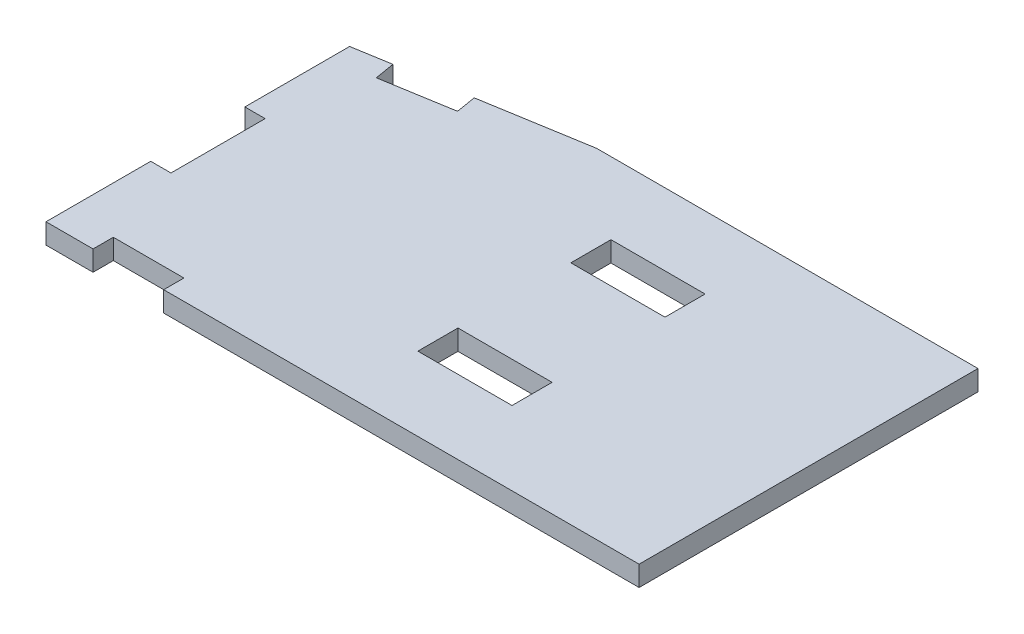
SolidWorks part; units mm, degrees
ref_plane "Front Plane" through (0, 0, 0) normal (0, 0, 1) x (1, 0, 0)
ref_plane "Top Plane" through (0, 0, 0) normal (0, 1, 0) x (1, 0, 0)
ref_plane "Right Plane" through (0, 0, 0) normal (1, 0, 0) x (0, 0, -1)
sketch "Sketch1" plane through (0, 0, 0) normal (0, 1, 0) x (1, 0, 0)
  line L0 (-99.45, 35.936) -> (-42.3, 45.461)
  line L1 (-47.5, 40) -> (47.5, 40)
  line L2 (-55, 32.5) -> (-55, -32.5)
  line L3 (-47.5, -40) -> (47.5, -40)
  line L4 (55, 32.5) -> (55, -32.5)
  line L5 (-55, 40) -> (55, -40) construction
  line L6 (-55, -40) -> (55, 40) construction
  line L7 (-99.45, 45.461) -> (60.57, 45.461)
  line L8 (-99.45, 45.461) -> (-99.45, -45.979)
  line L9 (-99.45, -45.979) -> (60.57, -45.979)
  line L10 (60.57, 45.461) -> (60.57, -45.979)
  line L11 (-99.45, 45.461) -> (60.57, -45.979) construction
  line L12 (-99.45, -45.979) -> (60.57, 45.461) construction
  arc A0 (47.5, -40) -> (55, -32.5) centre (47.5, -32.5) ccw
  arc A1 (55, 32.5) -> (47.5, 40) centre (47.5, 32.5) ccw
  arc A2 (-47.5, 40) -> (-55, 32.5) centre (-47.5, 32.5) ccw
  arc A3 (-47.5, -40) -> (-55, -32.5) centre (-47.5, -32.5) cw
  point P0 (0, 0)
  point P18 (0, 0)
  dimension "D3" = 7.5
  dimension "D1" = 80
  dimension "D2" = 110
  dimension "D4" = 5.461
  dimension "D5" = 44.45
  dimension "D6" = 5.979
  dimension "D7" = 91.44
  dimension "D8" = 5.57
  dimension "D9" = 160.02
  dimension "D10" = 9.525
  dimension "D11" = 57.15
extrude "Boss-Extrude1" add sketch "Sketch1" along normal blind 5.461 contours L10 L7 L0 L8 L9 L3 A3 L2 A2 L1 A1 L4 A0
sketch "Sketch2" plane through (0, 5.461, 0) normal (0, 1, 0) x (1, 0, 0)
  line L0 (-47.5, -40) -> (47.5, -40) construction
  line L1 (55, 32.5) -> (55, -32.5) construction
  line L2 (-47.5, 40) -> (47.5, 40) construction
  line L3 (-55, 32.5) -> (-55, -32.5) construction
  line L4 (-47.5, -40) -> (47.5, -40)
  line L5 (55, 32.5) -> (55, -32.5)
  line L6 (-47.5, 40) -> (47.5, 40)
  line L7 (-55, 32.5) -> (-55, -32.5)
  arc A0 (-55, -32.5) -> (-47.5, -40) centre (-47.5, -32.5) ccw construction
  arc A1 (47.5, -40) -> (55, -32.5) centre (47.5, -32.5) ccw construction
  arc A2 (55, 32.5) -> (47.5, 40) centre (47.5, 32.5) ccw construction
  arc A3 (-47.5, 40) -> (-55, 32.5) centre (-47.5, 32.5) ccw construction
  arc A4 (-55, -32.5) -> (-47.5, -40) centre (-47.5, -32.5) ccw
  arc A5 (47.5, -40) -> (55, -32.5) centre (47.5, -32.5) ccw
  arc A6 (55, 32.5) -> (47.5, 40) centre (47.5, 32.5) ccw
  arc A7 (-47.5, 40) -> (-55, 32.5) centre (-47.5, 32.5) ccw
extrude "Boss-Extrude2" add sketch "Sketch2" against normal up to surface (5.461 mm away) up to face at (-24.012, 0, -6.98)
sketch "Sketch3" plane through (0, 0, 0) normal (0, -1, 0) x (1, 0, 0)
  line L0 (-70.6374, -40.7381) -> (-89.4282, -37.6063)
  line L1 (-70.6374, -40.7381) -> (-69.7397, -35.3514)
  line L2 (-89.4282, -37.6063) -> (-88.5305, -32.2196)
  line L3 (-69.7397, -35.3514) -> (-88.5305, -32.2196)
  line L4 (-99.45, -35.936) -> (-42.3, -45.461) construction
  line L5 (-99.45, -7.6785) -> (-99.45, 17.7215)
  line L6 (-99.45, -7.6785) -> (-93.989, -7.6785)
  line L7 (-99.45, 17.7215) -> (-93.989, 17.7215)
  line L8 (-93.989, -7.6785) -> (-93.989, 17.7215)
  line L9 (-99.45, -35.936) -> (-99.45, 45.979) construction
  line L10 (-67.7, 45.979) -> (-86.75, 45.979)
  line L11 (-67.7, 45.979) -> (-67.7, 40.518)
  line L12 (-86.75, 45.979) -> (-86.75, 40.518)
  line L13 (-67.7, 40.518) -> (-86.75, 40.518)
  line L14 (-99.45, 45.979) -> (60.57, 45.979) construction
  point P18 (-99.45, 5.0215)
  dimension "D1" = 19.05
  dimension "D2" = 5.461
  dimension "D3" = 12.7
  dimension "D4" = 25.4
  dimension "D5" = 19.05
  dimension "D6" = 10.16
extrude "Cut-Extrude1" cut sketch "Sketch3" against normal through all
sketch "Sketch4" plane through (0, 5.461, 0) normal (0, 1, 0) x (1, 0, 0)
  line L0 (-6.35, -20.6375) -> (-6.35, 20.6375) construction
  line L1 (6.35, -26.0477) -> (-19.05, -26.0477)
  line L2 (6.35, -26.0477) -> (6.35, -15.2273)
  line L3 (6.35, -15.2273) -> (-19.05, -15.2273)
  line L4 (-19.05, -26.0477) -> (-19.05, -15.2273)
  line L5 (6.35, -26.0477) -> (-19.05, -15.2273) construction
  line L6 (6.35, -15.2273) -> (-19.05, -26.0477) construction
  line L7 (6.35, 15.2273) -> (-19.05, 15.2273)
  line L8 (6.35, 15.2273) -> (6.35, 26.0477)
  line L9 (6.35, 26.0477) -> (-19.05, 26.0477)
  line L10 (-19.05, 15.2273) -> (-19.05, 26.0477)
  line L11 (6.35, 15.2273) -> (-19.05, 26.0477) construction
  line L12 (6.35, 26.0477) -> (-19.05, 15.2273) construction
  point P0 (-6.35, -20.6375)
  point P5 (-6.35, 20.6375)
  point P10 (-6.35, 0)
  dimension "D1" = 10.8204
  dimension "D2" = 25.4
  dimension "D3" = 41.275
  dimension "D4" = 6.35
extrude "Cut-Extrude2" cut sketch "Sketch4" against normal through all
equation "\"D1@Sketch4\"=2*.213"
